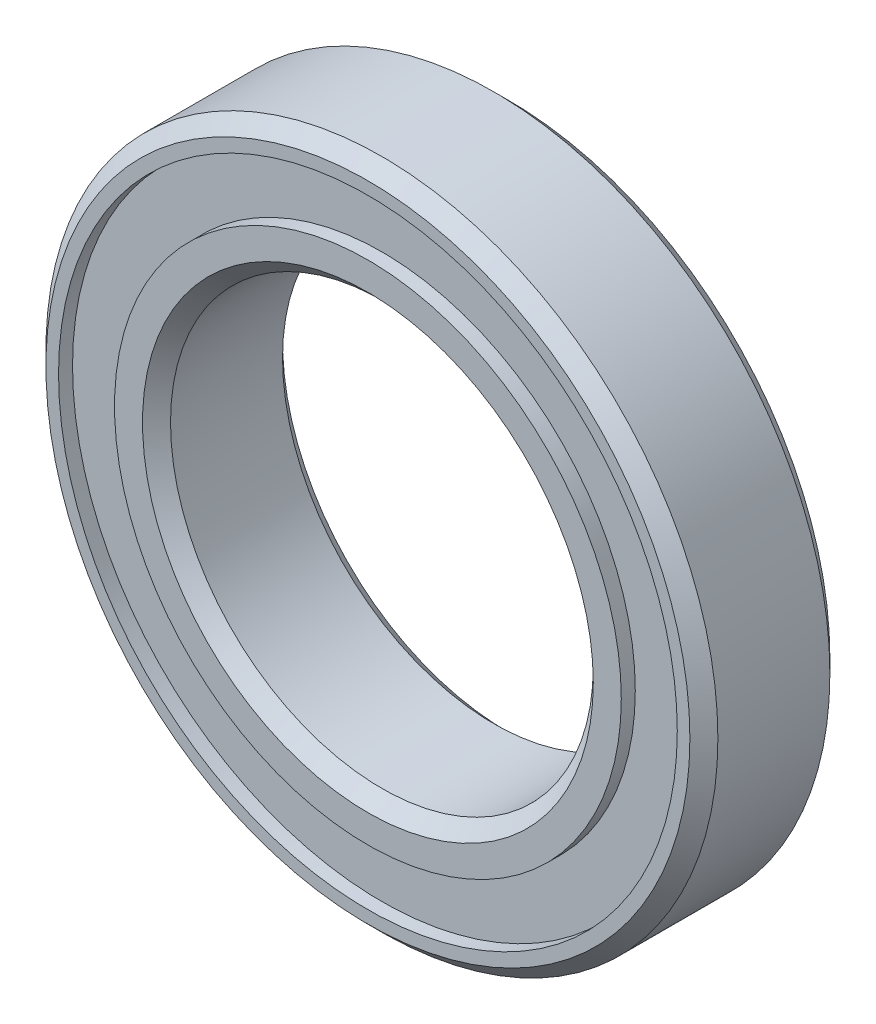
SolidWorks part; units mm, degrees
material "Gerais  - 6061-T6"
ref_plane "Plano frontal" through (0, 0, 0) normal (0, 0, 1) x (1, 0, 0)
ref_plane "Plano superior" through (0, 0, 0) normal (0, 1, 0) x (1, 0, 0)
ref_plane "Plano direito" through (0, 0, 0) normal (1, 0, 0) x (0, 0, -1)
sketch "Esboço1" plane through (0, 0, 0) normal (0, 0, 1) x (1, 0, 0)
  circle A0 centre (0, 0) radius 12
  circle A1 centre (0, 0) radius 7.55
  dimension "D1" = 24
  dimension "D2" = 15.1
extrude "Ressalto-extrusão1" add sketch "Esboço1" along normal blind 5
sketch "Esboço2" plane through (0, 0, 5) normal (0, 0, 1) x (1, 0, 0)
  circle A0 centre (0, 0) radius 11.05
  circle A1 centre (0, 0) radius 9.05
  circle A2 centre (0, 0) radius 7.55 construction
  circle A3 centre (0, 0) radius 12 construction
  point P4 (0, 7.55)
  point P5 (0, 9.05)
  point P8 (0, 12)
  point P9 (0, 11.05)
  dimension "D1" = 1.5
  dimension "D2" = 2
extrude "Corte-extrusão1" cut sketch "Esboço2" against normal blind 0.5 contours A0
sketch "Esboço3" plane through (0, 0, 0) normal (0, 0, -1) x (-1, 0, 0)
  circle A0 centre (0, 0) radius 9.05 construction
  circle A1 centre (0, 0) radius 11.05 construction
  circle A2 centre (0, 0) radius 9.05
  circle A3 centre (0, 0) radius 11.05
extrude "Corte-extrusão2" cut sketch "Esboço3" against normal blind 0.5
chamfer "Chanfro1" distance 0.5 angle 45 4 edges at (12, 0, 5) (12, 0, 0) (7.55, 0, 0) (7.55, 0, 5)
